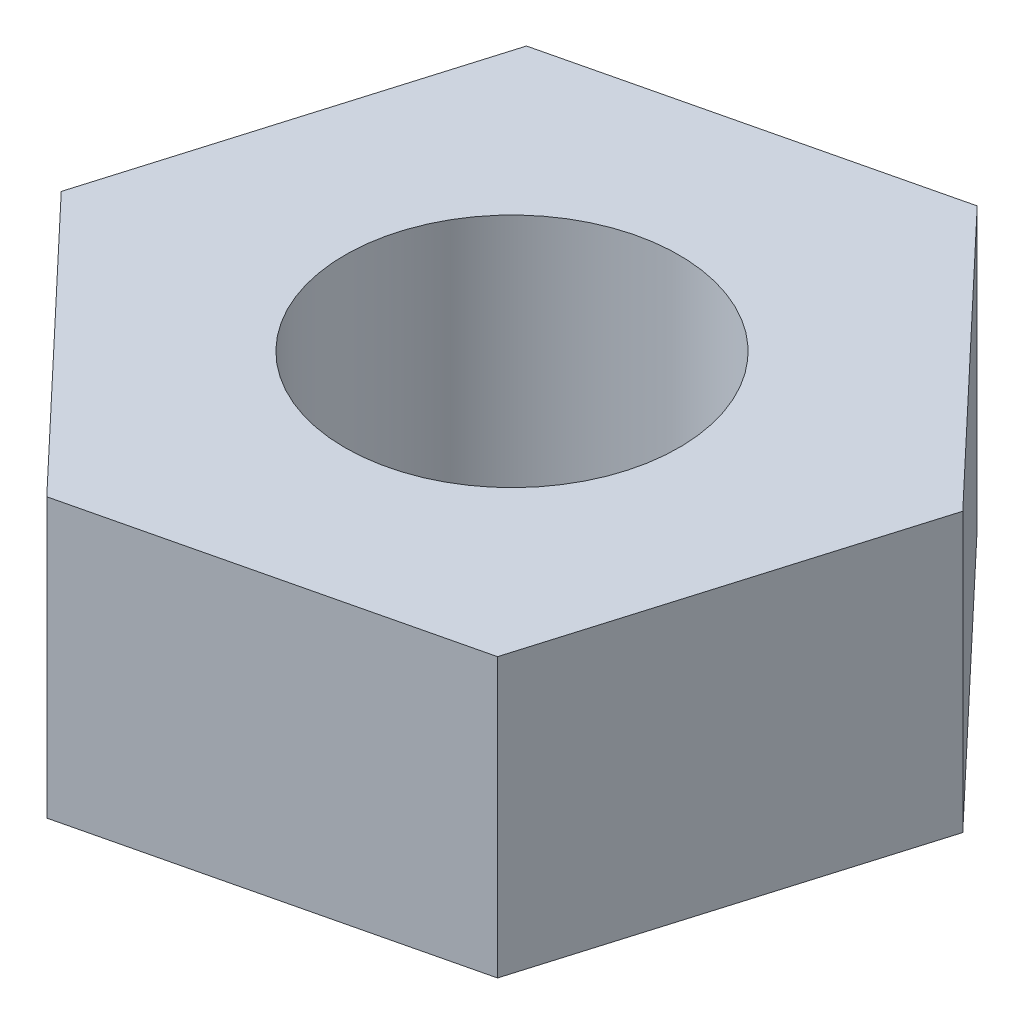
SolidWorks part; units mm, degrees
ref_plane "Front Plane" through (0, 0, 0) normal (0, 0, 1) x (1, 0, 0)
ref_plane "Top Plane" through (0, 0, 0) normal (0, 1, 0) x (1, 0, 0)
ref_plane "Right Plane" through (0, 0, 0) normal (1, 0, 0) x (0, 0, -1)
sketch "Sketch1" plane through (0, 0, 0) normal (0, 1, 0) x (1, 0, 0)
  line L1 (9.2416, -9.7618) -> (13.0748, 3.1225)
  line L2 (13.0748, 3.1225) -> (3.8332, 12.8843)
  line L3 (3.8332, 12.8843) -> (-9.2416, 9.7618)
  line L4 (-9.2416, 9.7618) -> (-13.0748, -3.1225)
  line L5 (-13.0748, -3.1225) -> (-3.8332, -12.8843)
  line L6 (-3.8332, -12.8843) -> (9.2416, -9.7618)
  circle A1 centre (0, 0) radius 11.6415 construction
extrude "Boss-Extrude1" add sketch "Sketch1" along normal blind 10
sketch "Sketch2" plane through (0, 10, 0) normal (0, 1, 0) x (1, 0, 0)
  circle A0 centre (0, 0) radius 6
  dimension "D1" = 12
extrude "Cut-Extrude1" cut sketch "Sketch2" against normal through all
